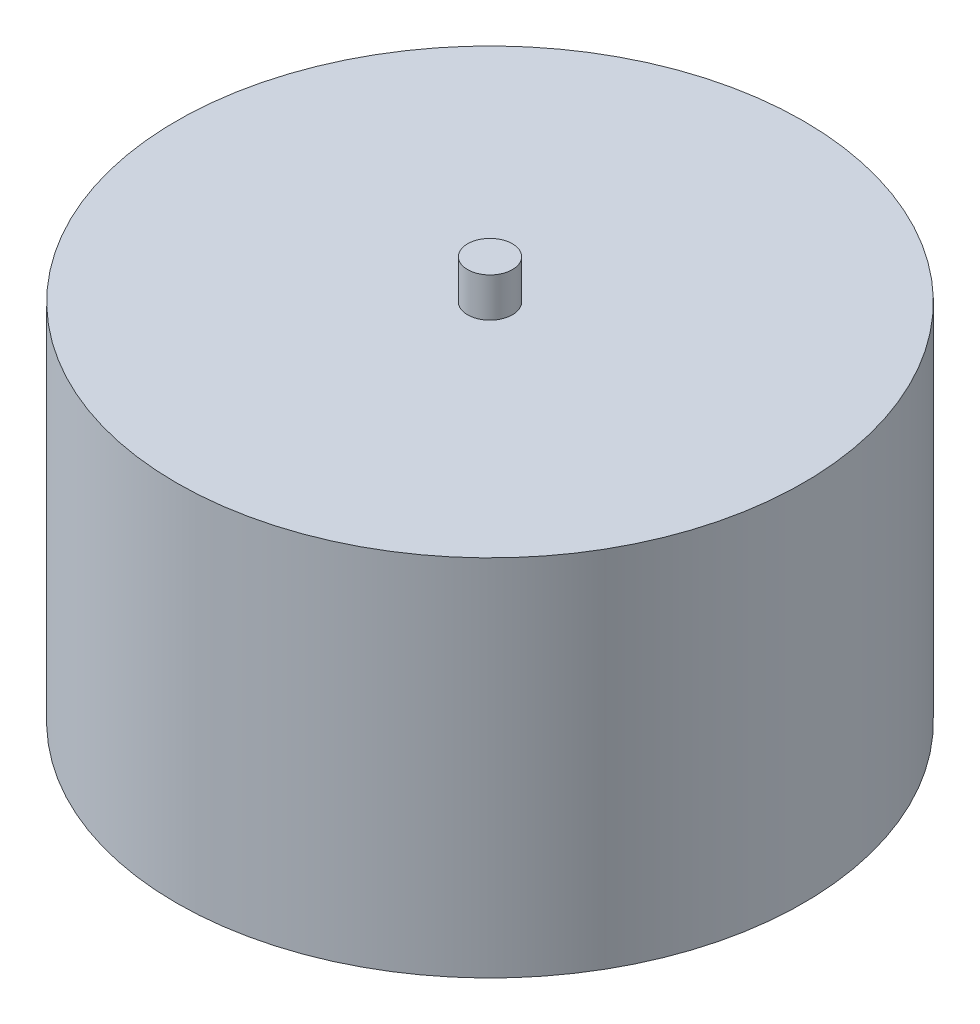
SolidWorks part; units mm, degrees
ref_plane "Front Plane" through (0, 0, 0) normal (0, 0, 1) x (1, 0, 0)
ref_plane "Top Plane" through (0, 0, 0) normal (0, 1, 0) x (1, 0, 0)
ref_plane "Right Plane" through (0, 0, 0) normal (1, 0, 0) x (0, 0, -1)
sketch "Sketch1" plane through (0, 0, 0) normal (0, 1, 0) x (1, 0, 0)
  circle A0 centre (0, 0) radius 28
  dimension "D1" = 56
extrude "Boss-Extrude1" add sketch "Sketch1" along normal blind 32.5
sketch "Sketch2" plane through (0, 32.5, 0) normal (0, 1, 0) x (1, 0, 0)
  circle A0 centre (0, 0) radius 2
  dimension "D1" = 4
extrude "Boss-Extrude2" add sketch "Sketch2" along normal blind 3.5
